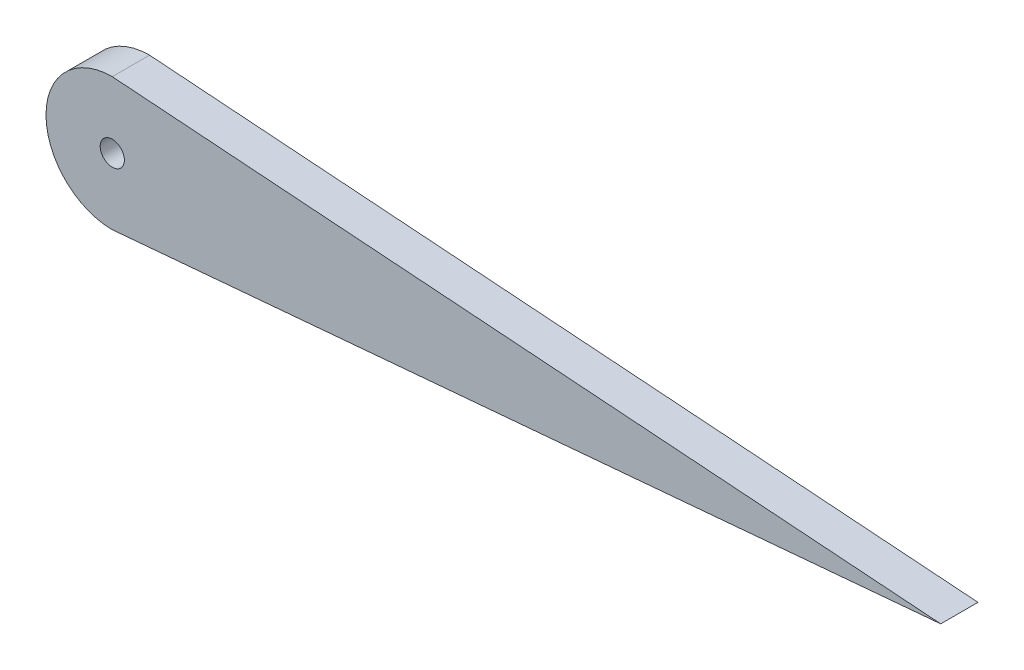
SolidWorks part; units mm, degrees
material "Balsa"
ref_plane "Front Plane" through (0, 0, 0) normal (0, 0, 1) x (1, 0, 0)
ref_plane "Top Plane" through (0, 0, 0) normal (0, 1, 0) x (1, 0, 0)
ref_plane "Right Plane" through (0, 0, 0) normal (1, 0, 0) x (0, 0, -1)
sketch "Sketch1" plane through (0, 0, 0) normal (0, 0, 1) x (1, 0, 0)
  line L1 (0, 4.064) -> (50.7984, 0.4062)
  line L2 (50.7984, 0.4062) -> (0, -4.064)
  arc A0 (0.5822, 4.0221) -> (0.7098, -4.0015) centre (0, 0) ccw
  circle A1 centre (0, 0) radius 0.7428
  dimension "D2" = 4.064
  dimension "D1" = 50.8
extrude "Boss-Extrude1" add sketch "Sketch1" along normal blind 2.286 contours L1 A0 L2 A1
